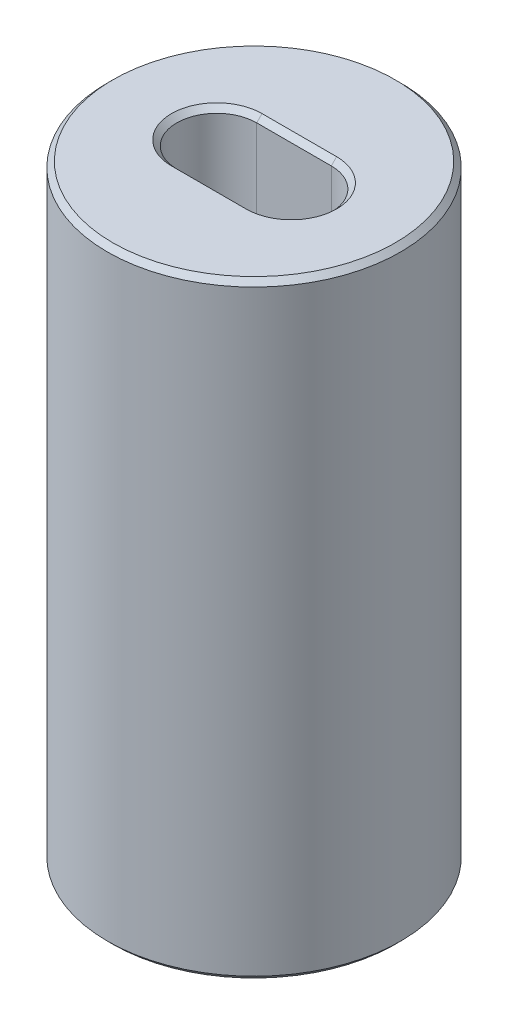
SolidWorks part; units mm, degrees
ref_plane "Front Plane" through (0, 0, 0) normal (0, 0, 1) x (1, 0, 0)
ref_plane "Top Plane" through (0, 0, 0) normal (0, 1, 0) x (1, 0, 0)
ref_plane "Right Plane" through (0, 0, 0) normal (1, 0, 0) x (0, 0, -1)
sketch "Sketch1" plane through (0, 0, 0) normal (0, 1, 0) x (1, 0, 0)
  line L0 (-0.7, 0) -> (0.7, 0) construction
  line L1 (-0.7, 0.75) -> (0.7, 0.75)
  line L2 (-0.7, -0.75) -> (0.7, -0.75)
  circle A0 centre (0, 0) radius 2.75
  circle A1 centre (0, 0) radius 1.45
  arc A2 (-0.7, 0.75) -> (-0.7, -0.75) centre (-0.7, 0) ccw
  arc A3 (0.7, -0.75) -> (0.7, 0.75) centre (0.7, 0) ccw
  point P6 (0, 0)
  point P11 (-1.45, 0)
  dimension "D1" = 5.5
  dimension "D2" = 2.9
  dimension "D3" = 0.75
extrude "main extrude" add sketch "Sketch1" along normal mid plane 11.4 contours A0 A1 | A3 L2 A2 A1 | A3 A1 A2 L1
chamfer "main chamfer" distance 0.1 angle 45 10 edges at (0, -5.7, 2.75) (0, 5.7, 2.75) (0, -5.7, 0.75) (-1.45, -5.7, 0) (1.45, -5.7, 0) (0, -5.7, -0.75) (0, 5.7, 0.75) (-1.45, 5.7, 0) (1.45, 5.7, 0) (0, 5.7, -0.75)
